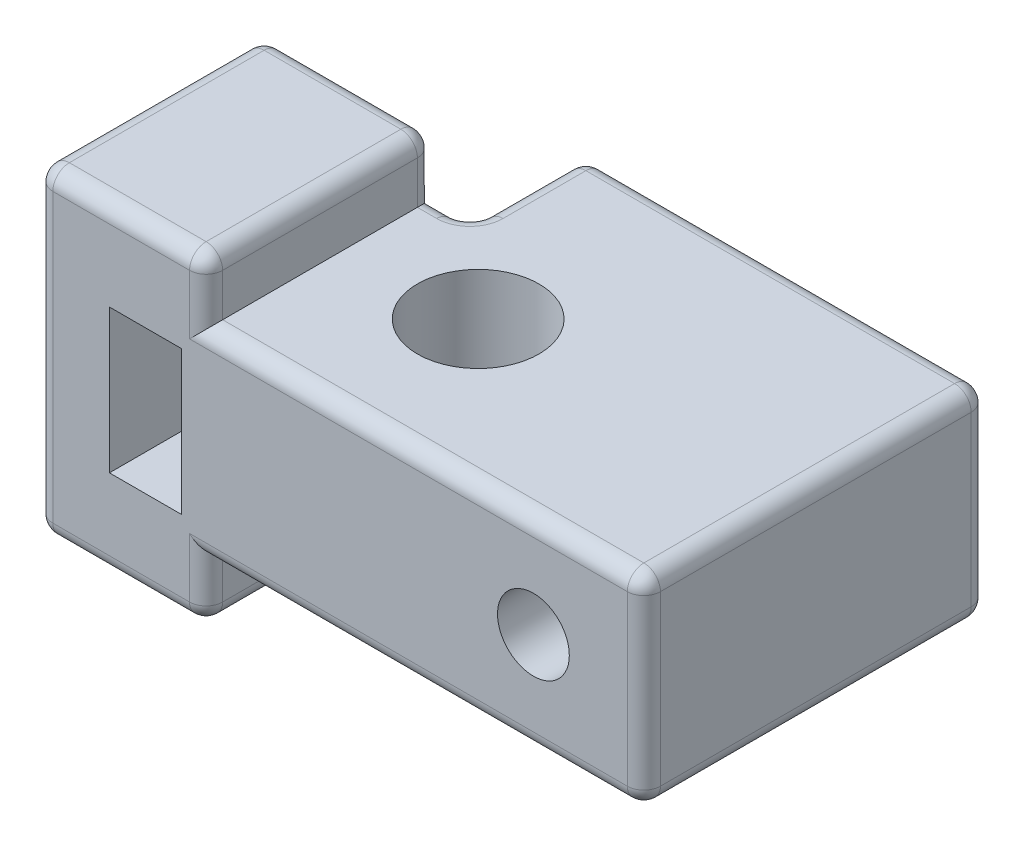
SolidWorks part; units mm, degrees
ref_plane "Front" through (0, 0, 0) normal (0, 0, 1) x (1, 0, 0)
ref_plane "Top" through (0, 0, 0) normal (0, 1, 0) x (1, 0, 0)
ref_plane "Right" through (0, 0, 0) normal (1, 0, 0) x (0, 0, -1)
sketch "Sketch1" plane through (0, 0, 0) normal (0, 1, 0) x (1, 0, 0)
  line L0 (-11.1125, 3.81) -> (-4.191, 3.81)
  line L1 (-4.191, 3.81) -> (-4.191, 9.144)
  line L3 (14.2875, 9.144) -> (14.2875, -6.6675)
  line L4 (14.2875, -6.6675) -> (-11.1125, -6.6675)
  line L5 (-11.1125, -6.6675) -> (-11.1125, 3.81)
  line L7 (0, 9.144) -> (0, 0) construction
  line L8 (-11.1125, 0) -> (0, 0) construction
  line L9 (14.2875, 9.144) -> (-4.191, 9.144)
  circle A0 centre (0, 0) radius 2.794
  point P2 (0, 0)
  dimension "D1" = 5.588
  dimension "D2" = 10.4775
  dimension "D3" = 11.1125
  dimension "D4" = 9.144
  dimension "D5" = 5.334
  dimension "D6" = 25.4
  dimension "D7" = 6.9215
extrude "Boss-Extrude1" add sketch "Sketch1" along normal mid plane 9.271
sketch "Sketch2" plane through (-11.1125, 0, 0) normal (-1, 0, 0) x (0, 0, 1)
  line L1 (-3.81, 4.6355) -> (6.6675, 4.6355)
  line L2 (-3.81, 4.6355) -> (-3.81, -4.6355)
  line L3 (-3.81, -4.6355) -> (6.6675, -4.6355)
  line L4 (6.6675, 4.6355) -> (6.6675, -4.6355)
extrude "Boss-Extrude2" add sketch "Sketch2" along normal blind 2.54
sketch "Sketch3" plane through (0, 0, 0) normal (0, 1, 0) x (1, 0, 0)
  line L8 (-5.842, -6.6675) -> (-13.6525, -6.6675)
  line L9 (-5.842, -6.6675) -> (-5.842, 3.81)
  line L10 (-5.842, 3.81) -> (-13.6525, 3.81)
  line L11 (-13.6525, -6.6675) -> (-13.6525, 3.81)
  line L12 (-13.6525, -6.6675) -> (-13.6525, 3.81) construction
  line L13 (14.2875, -6.6675) -> (-11.1125, -6.6675) construction
  line L14 (-11.1125, 3.81) -> (-4.191, 3.81) construction
  line L15 (0, 9.144) -> (0, 0) construction
  dimension "D2" = 5.842
extrude "Boss-Extrude3" add sketch "Sketch3" along normal mid plane 14.732
sketch "Sketch4" plane through (0, 0, -3.81) normal (0, 0, -1) x (-1, 0, 0)
  line L0 (3.6195, 0) -> (13.6525, 0) construction
  line L1 (6.985, 3.302) -> (10.287, 3.302)
  line L2 (6.985, 3.302) -> (6.985, -3.302)
  line L3 (6.985, -3.302) -> (10.287, -3.302)
  line L4 (10.287, 3.302) -> (10.287, -3.302)
  line L5 (13.6525, 7.366) -> (13.6525, -7.366) construction
  line L6 (4.191, 4.6355) -> (4.191, -4.6355) construction
  line L7 (8.636, 3.302) -> (8.636, -3.302) construction
  point P12 (8.636, 0)
  dimension "D1" = 3.302
  dimension "D2" = 6.604
  dimension "D3" = 4.445
extrude "Cut-Extrude1" cut sketch "Sketch4" against normal up to surface (10.4775 mm away) up to face at (-2.7622, 0, 6.6675)
sketch "Sketch5" plane through (0, 0, 6.6675) normal (0, 0, 1) x (1, 0, 0)
  line L0 (14.2875, 0) -> (9.2075, 0) construction
  line L1 (14.2875, 4.6355) -> (14.2875, -4.6355) construction
  circle A0 centre (9.2075, 0) radius 1.651
  dimension "D2" = 3.302
  dimension "D1" = 5.08
extrude "Cut-Extrude2" cut sketch "Sketch5" against normal up to surface (15.8115 mm away) up to face at (5.0483, 0, -9.144)
fillet "Fillet1" radius 0.762 28 edges at (-9.7472, 7.366, 6.6675) (-9.7472, 7.366, -3.81) (-13.6525, 7.366, 1.4287) (-13.6525, 0, 6.6675) (-13.6525, 0, -3.81) (-9.7472, -7.366, 6.6675) (-13.6525, -7.366, 1.4287) (-9.7472, -7.366, -3.81) (14.2875, 0, 6.6675) (14.2875, -4.6355, -1.2383) (4.2228, -4.6355, 6.6675) (14.2875, 4.6355, -1.2383) (4.2228, 4.6355, 6.6675) (-5.0165, -4.6355, -3.81) (-4.191, -4.6355, -6.477) (-5.0165, 4.6355, -3.81) (-4.191, 4.6355, -6.477) (-5.842, 7.366, 1.4288) (-5.842, 6.0008, 6.6675) (-5.842, -6.0008, 6.6675) (-5.842, 6.0008, -3.81) (-5.842, -7.366, 1.4288) (-5.842, -6.0008, -3.81) (-4.191, 0, -3.81) (14.2875, 0, -9.144) (5.0483, 4.6355, -9.144) (-4.191, 0, -9.144) (5.0483, -4.6355, -9.144)
